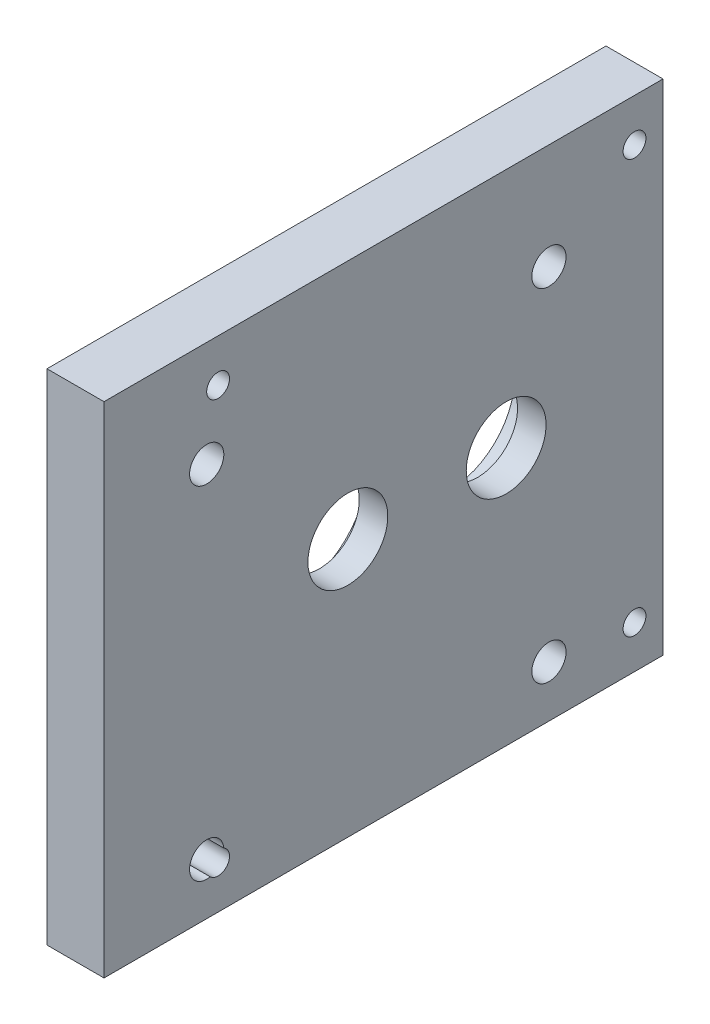
SolidWorks part; units mm, degrees
material "201 Annealed Stainless Steel (SS)"
ref_plane "Front Plane" through (0, 0, 0) normal (0, 0, 1) x (1, 0, 0)
ref_plane "Top Plane" through (0, 0, 0) normal (0, 1, 0) x (1, 0, 0)
ref_plane "Right Plane" through (0, 0, 0) normal (1, 0, 0) x (0, 0, -1)
sketch "Sketch1" plane through (114, 0, 0) normal (0, 1, 0) x (1, 0, 0)
  line L0 (-104, 0) -> (-114, 0) construction
  line L1 (-124, 98) -> (-104, 98)
  line L2 (-124, 98) -> (-124, -98)
  line L3 (-124, -98) -> (-104, -98)
  line L4 (-104, 98) -> (-104, -98)
  line L5 (-114, -96.25) -> (-114, 96.25) construction
  point P9 (-114, -98)
  dimension "D1" = 20
  dimension "D2" = 196
extrude "Boss-Extrude1" add sketch "Sketch1" along normal blind 175
sketch "Sketch2" plane through (-10, 0, 0) normal (-1, 0, 0) x (0, 0, 1)
  line L2 (0, -11) -> (0, 11) construction
  line L3 (0, -96.25) -> (0, 96.25) construction
  line L4 (98, 175) -> (98, 0) construction
  line L5 (-98, 0) -> (98, 0) construction
  line L6 (-98, 175) -> (-98, 0) construction
  circle A1 centre (12.5, 90.5) radius 27.5
  circle A2 centre (-43, 90.5) radius 23
  dimension "D1" = 55
  dimension "D2" = 46
  dimension "D5" = 58
  dimension "D6" = 63
  dimension "D7" = 90.5
  dimension "D8" = 32
  dimension "D3" = 12.5
  dimension "D4" = 43
extrude "Cut-Extrude1" cut sketch "Sketch2" against normal blind 10
sketch "Sketch3" plane through (0, 0, 0) normal (-1, 0, 0) x (0, 0, 1)
  circle A0 centre (12.5, 90.5) radius 14
  circle A1 centre (-43, 90.5) radius 14
  circle A2 centre (-43, 90.5) radius 23 construction
  circle A3 centre (12.5, 90.5) radius 27.5 construction
  dimension "D1" = 28
extrude "Cut-Extrude2" cut sketch "Sketch3" against normal through all
sketch "Sketch4" plane through (-10, 0, 0) normal (-1, 0, 0) x (0, 0, 1)
  circle A1 centre (58, 15) radius 4
  circle A2 centre (58, 15) radius 4
  circle A3 centre (-88, 15) radius 4
  circle A4 centre (-88, 15) radius 4
  circle A5 centre (-88, 160) radius 4
  circle A6 centre (-88, 160) radius 4
  circle A7 centre (58, 160) radius 4
  circle A8 centre (58, 160) radius 4
  dimension "D1" = 0
  dimension "D2" = 0
  dimension "D3" = 0
  dimension "D4" = 0
extrude "Cut-Extrude3" cut sketch "Sketch4" against normal through all
sketch "Sketch5" plane through (-10, 0, 0) normal (-1, 0, 0) x (0, 0, 1)
  line L0 (2, 149.9257) -> (2, 78) construction
  line L1 (2, 78) -> (116.2382, 78) construction
  line L2 (98, 175) -> (98, 0) construction
  line L3 (-98, 175) -> (98, 175) construction
  circle A0 centre (62, 138) radius 6
  circle A1 centre (62, 18) radius 6
  circle A2 centre (-58, 138) radius 6
  circle A3 centre (-58, 18) radius 6
  point P11 (17.3393, 89.6894)
  point P16 (116.2382, 82.0806)
  dimension "D1" = 12
  dimension "D2" = 132
  dimension "D3" = 132
  dimension "D4" = 30
  dimension "D5" = 31
extrude "Cut-Extrude4" cut sketch "Sketch5" against normal through all
ref_plane "Centre Bolts PLane  Vertical" through (0, 0, 2) normal (0, 0, 1) x (0, -1, 0)
ref_plane "Centre Bolts PLane Horizontal" through (0, 78, 0) normal (0, 1, 0) x (1, 0, 0)
